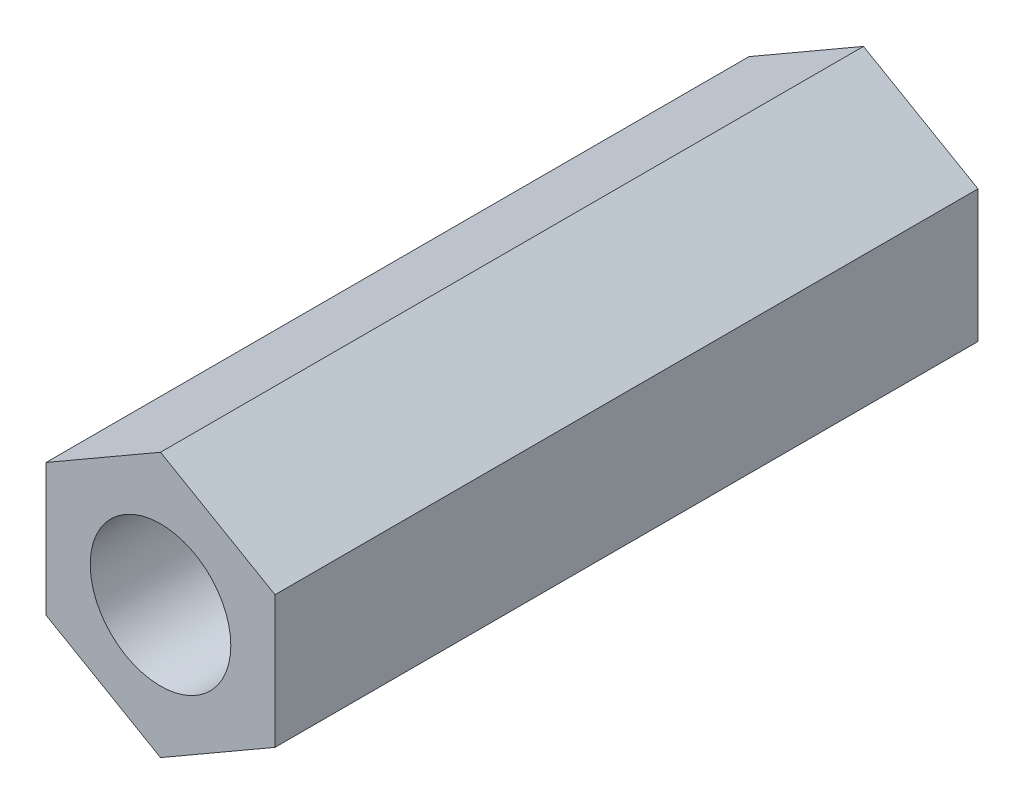
SolidWorks part; units mm, degrees
ref_plane "前视基准面" through (0, 0, 0) normal (0, 0, 1) x (1, 0, 0)
ref_plane "上视基准面" through (0, 0, 0) normal (0, 1, 0) x (1, 0, 0)
ref_plane "右视基准面" through (0, 0, 0) normal (1, 0, 0) x (0, 0, -1)
sketch "草图1" plane through (0, 0, 0) normal (0, 0, 1) x (1, 0, 0)
  line L1 (0, 2.8214) -> (-2.4434, 1.4107)
  line L2 (-2.4434, 1.4107) -> (-2.4434, -1.4107)
  line L3 (-2.4434, -1.4107) -> (0, -2.8214)
  line L4 (0, -2.8214) -> (2.4434, -1.4107)
  line L5 (2.4434, -1.4107) -> (2.4434, 1.4107)
  line L6 (2.4434, 1.4107) -> (0, 2.8214)
  circle A0 centre (0, 0) radius 1.5
  circle A1 centre (0, 0) radius 2.4434 construction
extrude "凸台-拉伸1" add sketch "草图1" along normal blind 15
